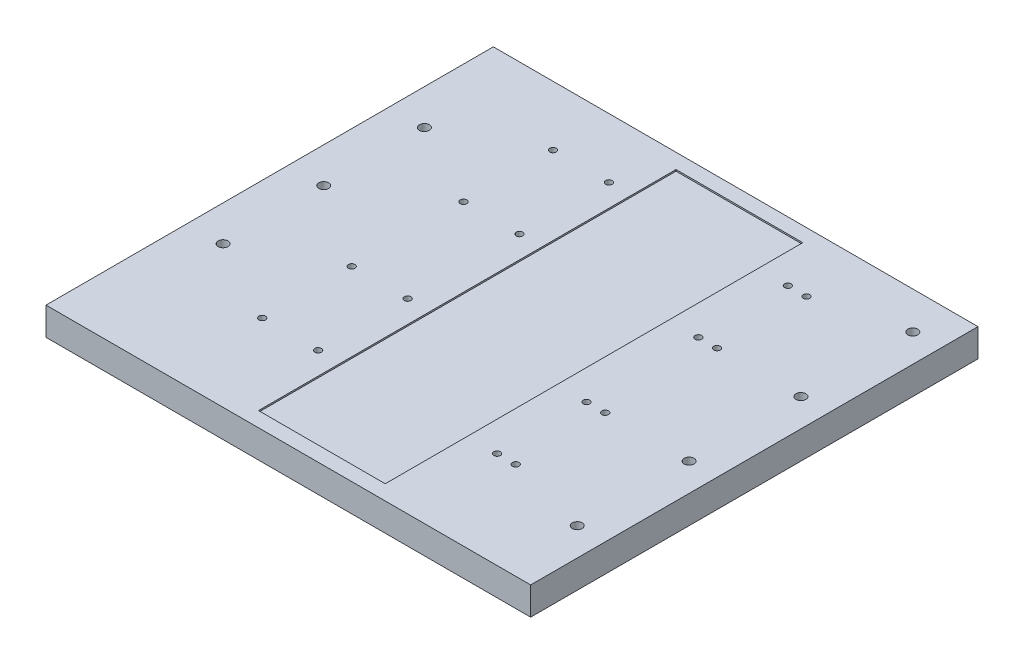
SolidWorks part; units mm, degrees
ref_plane "Front Plane" through (0, 0, 0) normal (0, 0, 1) x (1, 0, 0)
ref_plane "Top Plane" through (0, 0, 0) normal (0, 1, 0) x (1, 0, 0)
ref_plane "Right Plane" through (0, 0, 0) normal (1, 0, 0) x (0, 0, -1)
sketch "Sketch1" plane through (0, 0, 0) normal (0, 1, 0) x (1, 0, 0)
  line L1 (0, 0) -> (330.2, 0)
  line L2 (0, 0) -> (0, -304.8)
  line L3 (0, -304.8) -> (330.2, -304.8)
  line L4 (330.2, 0) -> (330.2, -304.8)
  dimension "D1" = 330.2
  dimension "D2" = 304.8
extrude "Boss-Extrude1" add sketch "Sketch1" along normal blind 19.05
sketch "Sketch2" plane through (0, 19.05, 0) normal (0, 1, 0) x (1, 0, 0)
  line L0 (0, -304.8) -> (330.2, -304.8) construction
  line L1 (134.62, -10.16) -> (220.98, -10.16)
  line L2 (134.62, -10.16) -> (134.62, -294.64)
  line L3 (134.62, -294.64) -> (220.98, -294.64)
  line L4 (220.98, -10.16) -> (220.98, -294.64)
  line L6 (0, 0) -> (0, -304.8) construction
  dimension "D1" = 86.36
  dimension "D2" = 284.48
  dimension "D3" = 10.16
  dimension "D4" = 134.62
extrude "Cut-Extrude1" cut sketch "Sketch2" against normal blind 1.016 contours L2 L1 L4 L3
sketch "Sketch3" plane through (0, 0, 0) normal (0, -1, 0) x (-1, 0, 0)
  line L0 (0, 0) -> (0, -304.8) construction
  line L1 (-330.2, 0) -> (0, 0) construction
  line L2 (-330.2, -304.8) -> (-330.2, 0) construction
  point P0 (-241.3, -40.64)
  point P1 (-254, -40.64)
  point P2 (-241.3, -101.6)
  point P3 (-254, -101.6)
  point P4 (-241.3, -177.8)
  point P5 (-254, -177.8)
  point P6 (-241.3, -238.76)
  point P7 (-254, -238.76)
  point P8 (-81.28, -40.64)
  point P9 (-119.38, -40.64)
  point P10 (-81.28, -101.6)
  point P11 (-119.38, -101.6)
  point P12 (-119.38, -177.8)
  point P13 (-81.28, -177.8)
  point P14 (-81.28, -238.76)
  point P15 (-119.38, -238.76)
  dimension "D1" = 12.7
  dimension "D2" = 38.1
  dimension "D3" = 81.28
  dimension "D4" = 40.64
  dimension "D5" = 76.2
  dimension "D6" = 60.96
  dimension "D7" = 60.96
  dimension "D8" = 76.2
hole_wizard "CBORE for #8 Socket Head Cap Screw1" positions "Sketch7" profile "Sketch8" counterbore size "#8" standard "ANSI Inch" end condition through all
sketch "Sketch7" plane through (0, 0, 0) normal (0, -1, 0) x (-1, 0, 0)
  point P0 (-241.3, -40.64)
  point P3 (-254, -40.64)
  point P6 (-254, -101.6)
  point P9 (-241.3, -101.6)
  point P12 (-241.3, -177.8)
  point P15 (-254, -177.8)
  point P18 (-254, -238.76)
  point P21 (-241.3, -238.76)
  point P24 (-119.38, -40.64)
  point P27 (-81.28, -40.64)
  point P30 (-81.28, -101.6)
  point P33 (-119.38, -101.6)
  point P36 (-119.38, -177.8)
  point P39 (-81.28, -177.8)
  point P42 (-81.28, -238.76)
  point P45 (-119.38, -238.76)
sketch "Sketch8" plane through (241.3, 0, 40.64) normal (1, 0, 0) x (0, 0, -1)
  line L0 (0, 0) -> (0, 19.05)
  line L1 (0, 19.05) -> (2.2479, 19.05)
  line L3 (2.2479, 19.05) -> (2.2479, 4.1656)
  line L4 (2.2479, 4.1656) -> (3.9687, 4.1656)
  line L5 (3.9687, 4.1656) -> (3.9687, 0)
  line L7 (3.9687, 0) -> (0, 0)
  line L11 (0, -6.35) -> (0, 107.95) construction
  dimension "Thru Hole Dia." = 4.4958
  dimension "Thru Hole Depth" = 19.05
  dimension "C'Bore Dia." = 7.9375
  dimension "C'Bore Depth" = 4.1656
sketch "Sketch9" plane through (0, 0, 0) normal (0, -1, 0) x (1, 0, 0)
  line L0 (330.2, 304.8) -> (330.2, 0) construction
  line L4 (0, 304.8) -> (330.2, 304.8) construction
  line L6 (0, 304.8) -> (330.2, 304.8) construction
  line L7 (0, 0) -> (0, 304.8) construction
  point P0 (311.15, 25.4)
  point P1 (311.15, 101.6)
  point P3 (311.15, 177.8)
  point P5 (24.13, 208.28)
  point P6 (24.13, 139.7)
  point P7 (24.13, 71.12)
  point P14 (311.15, 254)
  dimension "D1" = 19.05
  dimension "D2" = 165.1
  dimension "D3" = 24.13
  dimension "D5" = 68.58
  dimension "D6" = 68.58
  dimension "D7" = 76.2
  dimension "D8" = 76.2
  dimension "D9" = 76.2
  dimension "D10" = 50.8
hole_wizard "CBORE for 1/4 Binding Head Machine Screw1" positions "Sketch10" profile "Sketch12" counterbore size "1/4" standard "ANSI Inch" end condition through all
sketch "Sketch10" plane through (0, 0, 0) normal (0, -1, 0) x (-1, 0, 0)
  point P0 (-311.15, -25.4)
  point P3 (-311.15, -101.6)
  point P6 (-311.15, -177.8)
  point P9 (-311.15, -254)
  point P13 (-24.13, -71.12)
  point P16 (-24.13, -139.7)
  point P19 (-24.13, -208.28)
sketch "Sketch12" plane through (311.15, 0, 25.4) normal (1, 0, 0) x (0, 0, -1)
  line L0 (0, 0) -> (0, 19.05)
  line L1 (0, 19.05) -> (3.3782, 19.05)
  line L3 (3.3782, 19.05) -> (3.3782, 4.191)
  line L4 (3.3782, 4.191) -> (7.1437, 4.191)
  line L5 (7.1437, 4.191) -> (7.1437, 0)
  line L7 (7.1437, 0) -> (0, 0)
  line L11 (0, -6.35) -> (0, 107.95) construction
  dimension "Thru Hole Dia." = 6.7564
  dimension "Thru Hole Depth" = 19.05
  dimension "C'Bore Dia." = 14.2875
  dimension "C'Bore Depth" = 4.191
